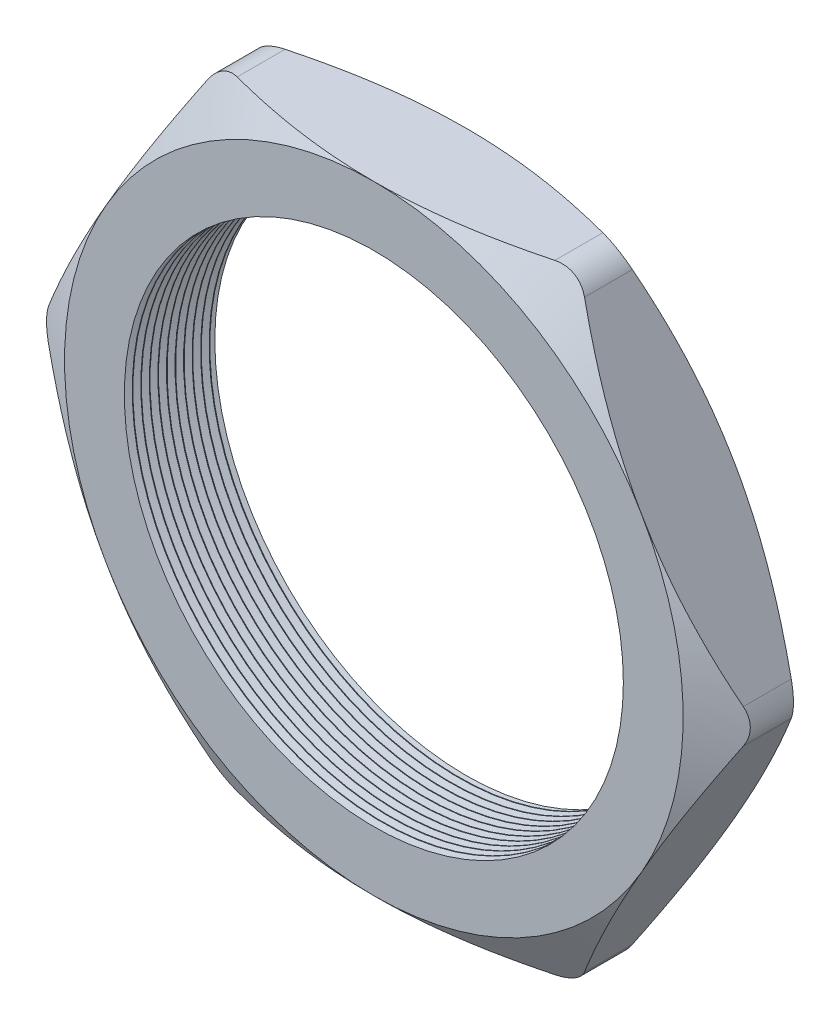
SolidWorks part; units mm, degrees
ref_plane "Front Plane" through (0, 0, 0) normal (0, 0, 1) x (1, 0, 0)
ref_plane "Top Plane" through (0, 0, 0) normal (0, 1, 0) x (1, 0, 0)
ref_plane "Right Plane" through (0, 0, 0) normal (1, 0, 0) x (0, 0, -1)
sketch "Sketch1" plane through (0, 0, 0) normal (0, 0, 1) x (1, 0, 0)
  line L1 (-26.5431, 0) -> (-13.2716, -22.987)
  line L2 (-13.2716, -22.987) -> (13.2716, -22.987)
  line L3 (13.2716, -22.987) -> (26.5431, 0)
  line L4 (26.5431, 0) -> (13.2716, 22.987)
  line L5 (13.2716, 22.987) -> (-13.2716, 22.987)
  line L6 (-13.2716, 22.987) -> (-26.5431, 0)
  circle A0 centre (0, 0) radius 22.987 construction
  circle A1 centre (0, 0) radius 18.542
  dimension "TS" = 37.084
  dimension "H" = 45.974
extrude "Extrude1" add sketch "Sketch1" along normal blind 6.858
sketch "Sketch2" plane through (0, 0, 6.858) normal (0, 0, 1) x (1, 0, 0)
  line L0 (13.2716, 22.987) -> (-13.2716, 22.987) construction
  circle A0 centre (0, 0) radius 22.987
extrude "Cut-Extrude1" cut sketch "Sketch2" against normal through all draft 60 flip side to cut
sketch "Sketch3" plane through (0, 0, 0) normal (0, 0, -1) x (-1, 0, 0)
  line L0 (-13.2716, 22.987) -> (13.2716, 22.987) construction
  circle A0 centre (0, 0) radius 22.987
extrude "Cut-Extrude2" cut sketch "Sketch3" against normal through all draft 60 flip side to cut
fillet "Fillet1" radius 2.54 6 edges at (26.5431, 0, 3.429) (13.2716, -22.987, 3.429) (-13.2716, -22.987, 3.429) (-26.5431, 0, 3.429) (-13.2716, 22.987, 3.429) (13.2716, 22.987, 3.429)
sketch "Sketch4" plane through (0, 0, 0) normal (0, 1, 0) x (1, 0, 0)
  line L0 (-18.542, -6.858) -> (-18.542, -6.2714)
  line L1 (-18.542, 0) -> (-18.542, -6.858) construction
  line L2 (-18.542, -6.2714) -> (-19.05, -6.5647)
  line L3 (-19.05, -6.5647) -> (-18.542, -6.858)
  dimension "D1" = 60
  dimension "D2" = 60
  dimension "D3" = 0.508
revolve "Cut-Revolve1" cut sketch "Sketch4" angle 360 about axis through (0, 0, 0) along (0, 0, 1)
pattern_linear "LPattern1" count 11 spacing 0.635 along (0, 0, -1) of "Cut-Revolve1"
